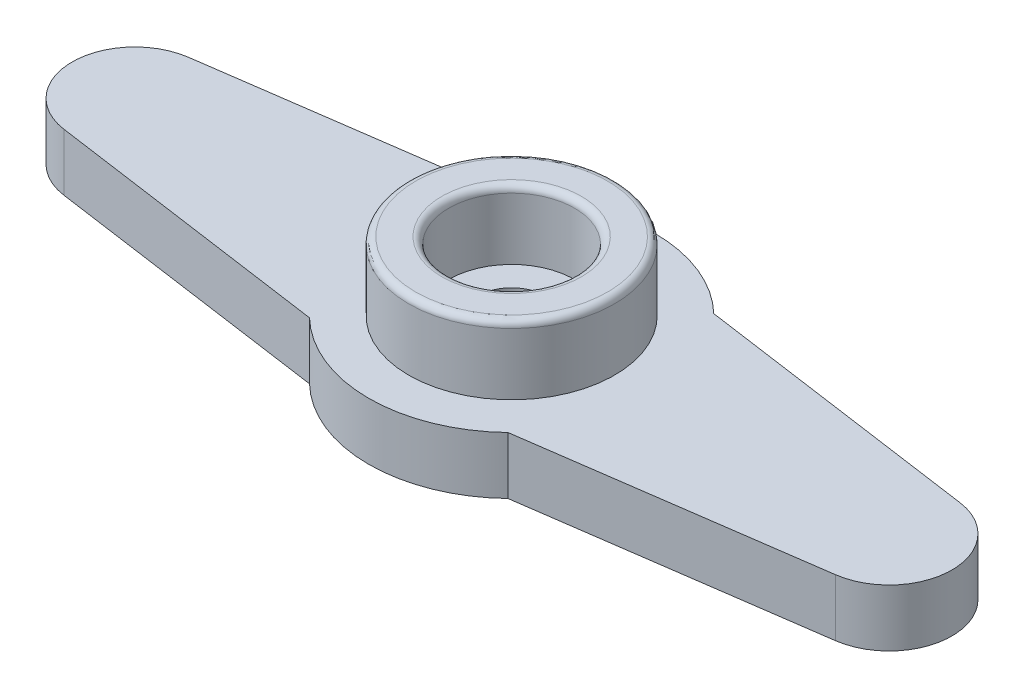
SolidWorks part; units mm, degrees
ref_plane "Alzado" through (0, 0, 0) normal (0, 0, 1) x (1, 0, 0)
ref_plane "Planta" through (0, 0, 0) normal (0, 1, 0) x (1, 0, 0)
ref_plane "Vista lateral" through (0, 0, 0) normal (1, 0, 0) x (0, 0, -1)
sketch "Croquis1" plane through (0, 0, 0) normal (0, 1, 0) x (1, 0, 0)
  line L0 (-19.25, 0) -> (19.25, 0) construction
  line L1 (16.8856, 2.7228) -> (4.3373, 4.5)
  line L2 (16.8856, -2.7228) -> (4.3373, -4.5)
  line L3 (-16.8548, 2.7228) -> (-4.3426, 4.4949)
  line L4 (-16.8548, -2.7228) -> (-4.3426, -4.4949)
  line L5 (4.3373, 4.5) -> (4.3373, -4.5) construction
  line L6 (4.3373, -4.5) -> (-4.3426, -4.4949) construction
  line L7 (-4.3426, -4.4949) -> (-4.3426, 4.4949) construction
  line L8 (-4.3426, 4.4949) -> (4.3373, 4.5) construction
  arc A0 (-4.3426, -4.4949) -> (4.3373, -4.5) centre (0, 0) ccw
  arc A1 (16.8856, -2.7228) -> (16.8856, 2.7228) centre (16.5, 0) ccw
  arc A2 (-16.8548, 2.7228) -> (-16.8548, -2.7228) centre (-16.4692, 0) ccw
  arc A3 (4.3373, 4.5) -> (-4.3426, 4.4949) centre (0, 0) ccw
  dimension "D1" = 12.5
  dimension "D3" = 5.5
  dimension "D4" = 9
  dimension "D2" = 38.5
extrude "Saliente-Extruir1" add sketch "Croquis1" along normal blind 2.5
sketch "Croquis2" plane through (0, 2.5, 0) normal (0, 1, 0) x (1, 0, 0)
  circle A0 centre (0, 0) radius 4.5
  circle A1 centre (0, 0) radius 2.75
  dimension "D1" = 9
  dimension "D2" = 5.5
extrude "Saliente-Extruir2" add sketch "Croquis2" along normal blind 3
sketch "Croquis3" plane through (0, 0, 0) normal (0, -1, 0) x (1, 0, 0)
  circle A0 centre (0, 0) radius 1.5
  dimension "D1" = 3
extrude "Cortar-Extruir1" cut sketch "Croquis3" against normal up to next
sketch "Croquis4" plane through (0, 0, 0) normal (0, -1, 0) x (1, 0, 0)
  circle A0 centre (0, 0) radius 2.8
  dimension "D1" = 5.6
extrude "Cortar-Extruir2" cut sketch "Croquis4" against normal offset from surface (1 mm away) 1.5 up to face at (0, 2.5, 1.5)
sketch "Croquis5" plane through (0, 0, 0) normal (0, -1, 0) x (1, 0, 0)
  circle A0 centre (0, 0) radius 4.5
  circle A1 centre (0, 0) radius 3.5
  dimension "D1" = 9
  dimension "D2" = 7
extrude "Cortar-Extruir3" cut sketch "Croquis5" against normal blind 0.5
fillet "Redondeo1" radius 0.3 5 edges at (0, 0, -4.5) (0, 0, -2.8) (0, 0, -3.5) (0, 5.5, 2.75) (0, 5.5, 4.5)
